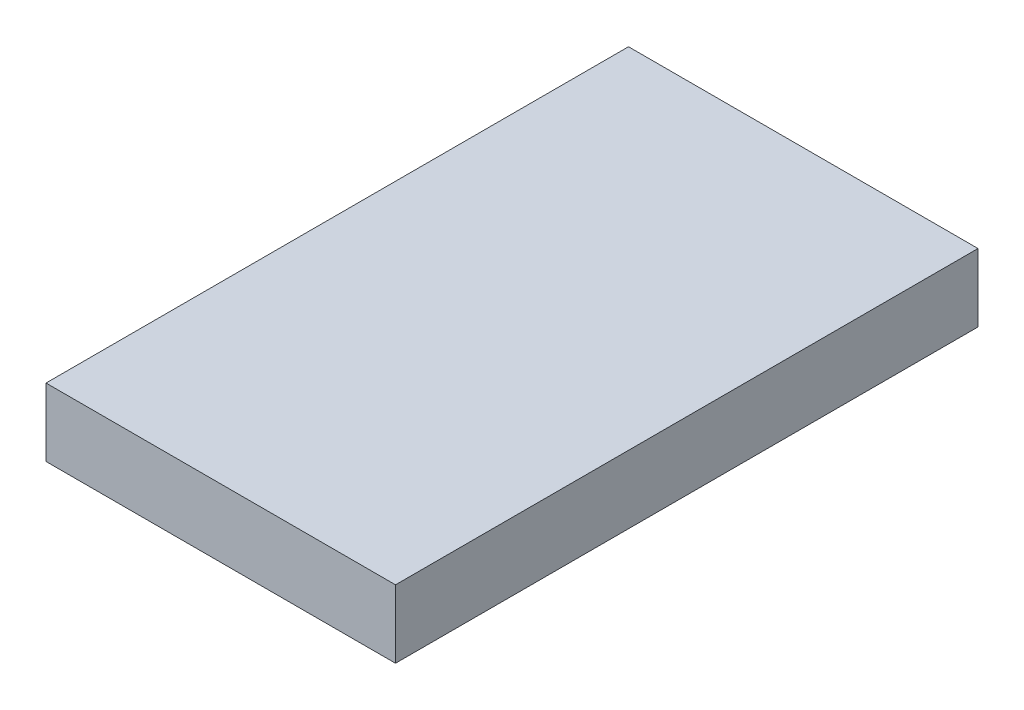
SolidWorks part; units mm, degrees
ref_plane "Front Plane" through (0, 0, 0) normal (0, 0, 1) x (1, 0, 0)
ref_plane "Top Plane" through (0, 0, 0) normal (0, 1, 0) x (1, 0, 0)
ref_plane "Right Plane" through (0, 0, 0) normal (1, 0, 0) x (0, 0, -1)
sketch "Sketch1" plane through (0, 0, 0) normal (0, 1, 0) x (1, 0, 0)
  line L1 (-18, 30) -> (18, 30)
  line L2 (-18, 30) -> (-18, -30)
  line L3 (-18, -30) -> (18, -30)
  line L4 (18, 30) -> (18, -30)
  line L5 (-18, 30) -> (18, -30) construction
  line L6 (-18, -30) -> (18, 30) construction
  point P0 (0, 0)
  dimension "D1" = 36
  dimension "D2" = 60
extrude "Boss-Extrude1" add sketch "Sketch1" along normal mid plane 7
